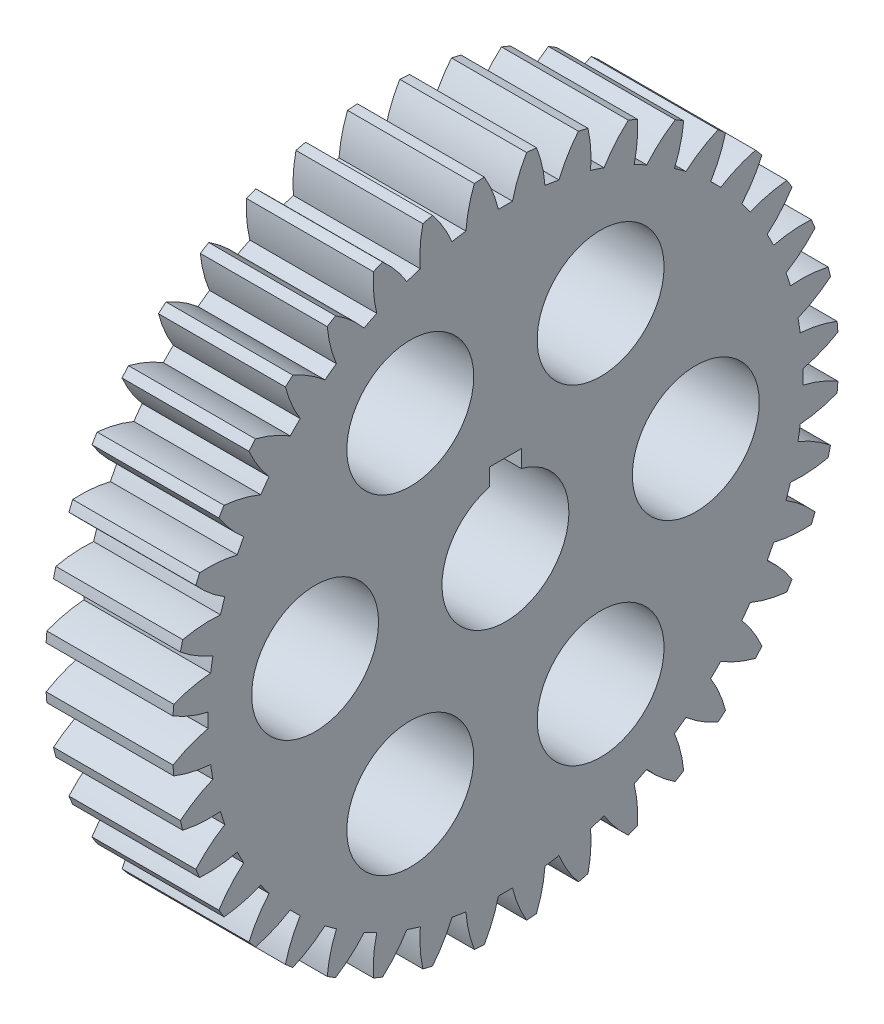
SolidWorks part; units mm, degrees
ref_plane "Plane1" through (0, 0, 0) normal (0, 0, 1) x (1, 0, 0)
ref_plane "Plane2" through (0, 0, 0) normal (0, 1, 0) x (1, 0, 0)
ref_plane "Plane3" through (0, 0, 0) normal (1, 0, 0) x (0, 0, -1)
sketch "HoldingSke" plane through (0, 0, 0) normal (0, 1, 0) x (1, 0, 0)
  line L0 (0, 0) -> (311.3205, -261.2289)
  line L1 (-15, 0) -> (100, 0) construction
  line L2 (0, 0) -> (-2.1039, 2.3779)
  line L3 (0, 0) -> (-11.863, 4.5341)
  line L4 (0, 0) -> (6.6156, 5.5511)
  line L5 (0, 0) -> (-47.5972, -17.7524)
  line L6 (0, 0) -> (-10.5278, -7.1032)
  line L7 (-2.1039, 2.3779) -> (8.8308, 51.9871)
  line L8 (-76.2, 54.61) -> (-62.3824, 54.61)
  line L9 (-71.009, 38.7566) -> (-53.1078, 45.2721)
  line L10 (-76.2, 71.12) -> (104.1128, 71.12)
  line L11 (0, 0) -> (-12.7, 0)
  line L12 (-76.2, 101.6) -> (-76.1428, 101.6)
  line L13 (24.9733, 27.94) -> (52.9518, 28.4284)
  line L14 (24.9733, 27.94) -> (24.9746, 27.94)
  line L15 (24.9733, 27.94) -> (100.4006, 29.5858)
  circle A0 centre (0, 0) radius 6.35
  circle A1 centre (0, 0) radius 29.7644
  circle A2 centre (0, 0) radius 38.1
  circle A3 centre (0, 0) radius 6.35
  dimension "MHD" = 59.5287
  dimension "Hub_dia" = 76.2
  dimension "Bore" = 12.7
  dimension "MBD" = 12.7
  dimension "Num_teeth" = 40
  dimension "Pitch" = 406.4
  dimension "Overall_len" = 50.8
  dimension "Show_teeth" = 40
  dimension "Thickness" = 12.7
  dimension "OAL" = 50.8001
  dimension "T_dim" = 13.8176
  dimension "Ap" = 20
  dimension "H" = 19.05
  dimension "Pitch_radius" = 180.3128
  dimension "Width" = 12.7
  dimension "Backlash" = 0.0571
  dimension "Addendum_fac" = 1
  dimension "Dedendum_fac" = 1.25
  dimension "Clearance_fac" = 0.25
  dimension "Dedendum_add" = 0.0013
sketch "BasProSke" plane through (0, 0, 0) normal (0, 1, 0) x (1, 0, 0)
  line L0 (-10, 0) -> (60, 0) construction
  line L1 (0, 0) -> (0, 33.3375)
  line L2 (0, 0) -> (12.7, 0)
  line L3 (12.7, 0) -> (12.7, 33.3375)
  line L4 (12.7, 33.3375) -> (0, 33.3375)
  dimension "Thickness" = 12.7
  dimension "Diameter" = 66.675
revolve "Base-Revolve" add sketch "BasProSke" angle 360 about L0
sketch "TooCutSke" plane through (0, 0, 0) normal (1, 0, 0) x (0, 0, -1)
  line L1 (0, 0) -> (0, 107) construction
  line L2 (0, 0) -> (-1.3465, 31.7214) construction
  line L3 (0, 0) -> (-4.9789, 63.263) construction
  line L4 (-1.3465, 31.7214) -> (-2.4895, 31.6315) construction
  arc A0 (0.7071, 29.756) -> (-0.7071, 29.756) centre (0, 0) ccw
  arc A1 (2.1363, 33.2944) -> (-2.1363, 33.2944) centre (0, 0) ccw
  circle A2 centre (0, 0) radius 31.75 construction
  circle A3 centre (0, 0) radius 29.8352 construction
  arc A4 (-0.7071, 29.756) -> (-2.1363, 33.2944) centre (-13.0638, 26.8231) ccw
  arc A5 (2.1363, 33.2944) -> (0.7071, 29.756) centre (13.0638, 26.8231) ccw
  dimension "Root_dia" = 59.5287
  dimension "Overcut_dia" = 66.7258
  dimension "Pitch_dia" = 63.5
  dimension "Base_dia" = 59.6705
  dimension "Flank_rad" = 12.7
  dimension "Half_ang" = 4.5
  dimension "Half_CT" = 1.1465
extrude "ToothCut" cut sketch "TooCutSke" along normal through all
fillet "Breaks" [suppressed] radius 0.0318
fillet "RootFillets" [suppressed] radius 0.3981
pattern_circular "TeethCuts" count 40 every 9 about axis through (-10, 0, 0) along (1, 0, 0) of "ToothCut", "RootFillets", "Breaks"
sketch "HubNeaOneSke" plane through (0, 0, 0) normal (-1, 0, 0) x (0, 0, 1)
  circle A0 centre (0, 0) radius 29.7644
  dimension "Diameter" = 59.5287
extrude "HubNearOne" [suppressed] add sketch "HubNeaOneSke" along normal blind 38.1001
sketch "HubNeaBotSke" plane through (0, 0, 0) normal (-1, 0, 0) x (0, 0, 1)
  circle A0 centre (0, 0) radius 29.7644
  dimension "Diameter" = 59.5287
extrude "HubNearBoth" [suppressed] add sketch "HubNeaBotSke" along normal blind 19.05
ref_plane "FarPln" through (12.7, 0, 0) normal (1, 0, 0) x (0, 0, -1)
sketch "HubFarSke" plane through (12.7, 0, 0) normal (1, 0, 0) x (0, 0, -1)
  circle A0 centre (0, 0) radius 29.7644
  dimension "Diameter" = 59.5287
extrude "HubFar" [suppressed] add sketch "HubFarSke" along normal blind 19.05
sketch "BorSke" plane through (0, 0, 0) normal (1, 0, 0) x (0, 0, -1)
  circle A0 centre (0, 0) radius 6.35
  dimension "Diameter" = 12.7
extrude "Bore" cut sketch "BorSke" along normal mid plane 101.6001
sketch "KeySke" plane through (0, 0, 0) normal (1, 0, 0) x (0, 0, -1)
  line L0 (-1.5875, 0) -> (-1.5875, 7.4676)
  line L1 (-1.5875, 7.4676) -> (1.5875, 7.4676)
  line L2 (1.5875, 7.4676) -> (1.5875, 0)
  line L3 (0, 0) -> (0, 34) construction
  line L4 (-1.5875, 0) -> (1.5875, 0)
  dimension "Offset" = 7.4676
  dimension "Width" = 3.175
extrude "Keyway" cut sketch "KeySke" along normal mid plane 101.6001
pattern_circular "Keyway2" [suppressed] count 2 every 90 about axis through (-10, 0, 0) along (1, 0, 0)
sketch "Sketch1" plane through (12.7, 0, 0) normal (1, 0, 0) x (0, 0, -1)
  line L0 (-1.5875, 7.4676) -> (-1.5875, 7.874)
  line L1 (1.5875, 7.4676) -> (1.5875, 7.874)
  line L2 (-1.5875, 7.874) -> (1.5875, 7.874)
extrude "Cut-Extrude1" cut sketch "Sketch1" against normal through all and the other way through all
sketch "Sketch2" plane through (12.7, 0, 0) normal (1, 0, 0) x (0, 0, -1)
  circle A1 centre (-19.05, 0) radius 6.35
  point P2 (0, 0)
  point P6 (0, 0)
extrude "Cut-Extrude3" cut sketch "Sketch2" against normal through all contours A1
pattern_circular "CirPattern1" count 6 over 360 about axis through (0, 0, 0) along (1, 0, 0) of "Cut-Extrude3"
equation "' \"Pitch@HoldingSke\" = 4"
equation "' \"Num_teeth@HoldingSke\" = 12"
equation "' \"Ap@HoldingSke\" =  20"
equation "' \"Ap@HoldingSke\" = 20"
equation "' \"Width@HoldingSke\" = 0.5"
equation "' \"Hub_dia@HoldingSke\"= 1"
equation "' \"Hub_dia@HoldingSke\" = 1"
equation "' \"Overall_len@HoldingSke\" = 1.0"
equation "' \"Bore@HoldingSke\" = 0.75"
equation "' \"T_dim@HoldingSke\" = 0.85"
equation "' \"Width@KeySke\" = 0.25"
equation "' \"Show_teeth@HoldingSke\" = 13"
equation "' \"Backlash@HoldingSke\" = 0.009"
equation "' \"Addendum_fac@HoldingSke\" = 1.0"
equation "' \"Dedendum_fac@HoldingSke\" = 1.25"
equation "' \"Dedendum_add@HoldingSke\" = 0.00005"
equation "' \"Clearance_fac@HoldingSke\" = 0.25"
equation "' \"Pitch@HoldingSke\" = 0.5"
equation "' \"Num_teeth@HoldingSke\" = 23"
equation "' \"Show_teeth@HoldingSke\" = 23"
equation "' \"Backlash@HoldingSke\" = 0.0375"
equation "\"Overcut_dia@TooCutSke\" = (\"Num_teeth@HoldingSke\" + 2 * \"Addendum_fac@HoldingSke\") / \"Pitch@HoldingSke\" + 0.002"
equation "\"Pitch_dia@TooCutSke\" = \"Num_teeth@HoldingSke\" / \"Pitch@HoldingSke\""
equation "\"Base_dia@TooCutSke\" = \"Num_teeth@HoldingSke\" / \"Pitch@HoldingSke\" * cos((\"Ap@HoldingSke\"  * 3.14159265 / 180))"
equation "\"Root_dia@TooCutSke\" = (\"Num_teeth@HoldingSke\" + 2) / \"Pitch@HoldingSke\" - 2 * (\"Addendum_fac@HoldingSke\" + \"Dedendum_fac@HoldingSke\") / \"Pitch@HoldingSke\" - \"Dedendum_add@HoldingSke\" * 2"
equation "\"Half_ang@TooCutSke\" = 180 / \"Num_teeth@HoldingSke\""
equation "\"Half_CT@TooCutSke\" = \"Num_teeth@HoldingSke\" / \"Pitch@HoldingSke\" * sin((3.14159265 / 2 / \"Num_teeth@HoldingSke\")) / 2 - 7 * \"Backlash@HoldingSke\" / 4"
equation "\"Flank_rad@TooCutSke\" = \"Num_teeth@HoldingSke\" / \"Pitch@HoldingSke\" / 5"
equation "\"Radius@RootFillets\" = \"Clearance_fac@HoldingSke\" / \"Pitch@HoldingSke\" + \"Dedendum_add@HoldingSke\""
equation "\"Break_rad@Breaks\" = 0.02 / \"Pitch@HoldingSke\""
equation "\"Thickness@HoldingSke\" = \"Width@HoldingSke\""
equation "\"OAL@HoldingSke\" = \"Thickness@HoldingSke\""
equation "\"MHD@HoldingSke\" = (\"Num_teeth@HoldingSke\" + 2) / \"Pitch@HoldingSke\" - 2 * (\"Addendum_fac@HoldingSke\" + \"Dedendum_fac@HoldingSke\")  / \"Pitch@HoldingSke\" - \"Dedendum_add@HoldingSke\" * 2"
equation "\"MBD@HoldingSke\" = (\"Num_teeth@HoldingSke\" + 2) / \"Pitch@HoldingSke\" - 2 * (\"Addendum_fac@HoldingSke\" + \"Dedendum_fac@HoldingSke\")  / \"Pitch@HoldingSke\" - \"Dedendum_add@HoldingSke\" * 2 - 0.002"
equation "\"MHD@HoldingSke\" = ((sgn( \"MHD@HoldingSke\" - \"Hub_dia@HoldingSke\" )-1)*( \"MHD@HoldingSke\" - \"Hub_dia@HoldingSke\" ))/-2+ \"Hub_dia@HoldingSke\""
equation "\"MBD@HoldingSke\" = ((sgn( \"MBD@HoldingSke\" - \"Bore@HoldingSke\" )-1)*( \"MBD@HoldingSke\" - \"Bore@HoldingSke\" ))/-2+ \"Bore@HoldingSke\""
equation "\"OAL@HoldingSke\" = ((sgn( \"OAL@HoldingSke\" - \"Overall_len@HoldingSke\" )+1)*( \"OAL@HoldingSke\" - \"Overall_len@HoldingSke\" ))/2 + \"Overall_len@HoldingSke\" + 0.000002"
equation "\"Num_teeth@TeethCuts\" = int( \"Show_teeth@HoldingSke\" ) + 1"
equation "\"Num_teeth@TeethCuts\" = ((sgn( \"Num_teeth@TeethCuts\" - \"Num_teeth@HoldingSke\" )-1)*( \"Num_teeth@TeethCuts\" - \"Num_teeth@HoldingSke\" ))/-2+ \"Num_teeth@HoldingSke\""
equation "\"Num_teeth@TeethCuts\" = ((sgn( \"Num_teeth@TeethCuts\" - 2.0)+1)*( \"Num_teeth@TeethCuts\" - 2.0))/2 +2.0"
equation "\"Angle@TeethCuts\" = 360.0 / \"Num_teeth@HoldingSke\""
equation "\"Diameter@BasProSke\" = (\"Num_teeth@HoldingSke\" + 2 * \"Addendum_fac@HoldingSke\") / \"Pitch@HoldingSke\""
equation "\"Thickness@BasProSke\"  = \"Thickness@HoldingSke\""
equation "' \"Fillet_rad@BasProSke\" =  \"Thickness@HoldingSke\" * 0.05"
equation "' \"Fillet_rad@BasProSke\" = \"Thickness@HoldingSke\" * 0.05"
equation "\"MHD@HoldingSke\" = ((sgn( \"MHD@HoldingSke\" - \"Root_dia@TooCutSke\" )-1)*( \"MHD@HoldingSke\" - \"Root_dia@TooCutSke\" ))/-2+ \"Root_dia@TooCutSke\""
equation "\"Diameter@HubNeaOneSke\" = \"MHD@HoldingSke\""
equation "\"Length@HubNearOne\" = \"OAL@HoldingSke\" - \"Thickness@BasProSke\""
equation "\"Diameter@HubNeaBotSke\" = \"MHD@HoldingSke\""
equation "\"Length@HubNearBoth\" = ( \"OAL@HoldingSke\" - \"Thickness@BasProSke\" ) / 2.0"
equation "\"Thickness@FarPln\" = \"Thickness@BasProSke\""
equation "\"Diameter@HubFarSke\" = \"MHD@HoldingSke\""
equation "\"Length@HubFar\" = ( \"OAL@HoldingSke\" - \"Thickness@BasProSke\" ) / 2.0"
equation "\"Diameter@BorSke\" = \"MBD@HoldingSke\""
equation "\"D1@Bore\" = \"OAL@HoldingSke\" * 2.0"
equation "\"D1@Keyway\" = \"OAL@HoldingSke\" * 2.0"
equation "\"Offset@KeySke\" = \"T_dim@HoldingSke\" - \"MBD@HoldingSke\" / 2.0"
